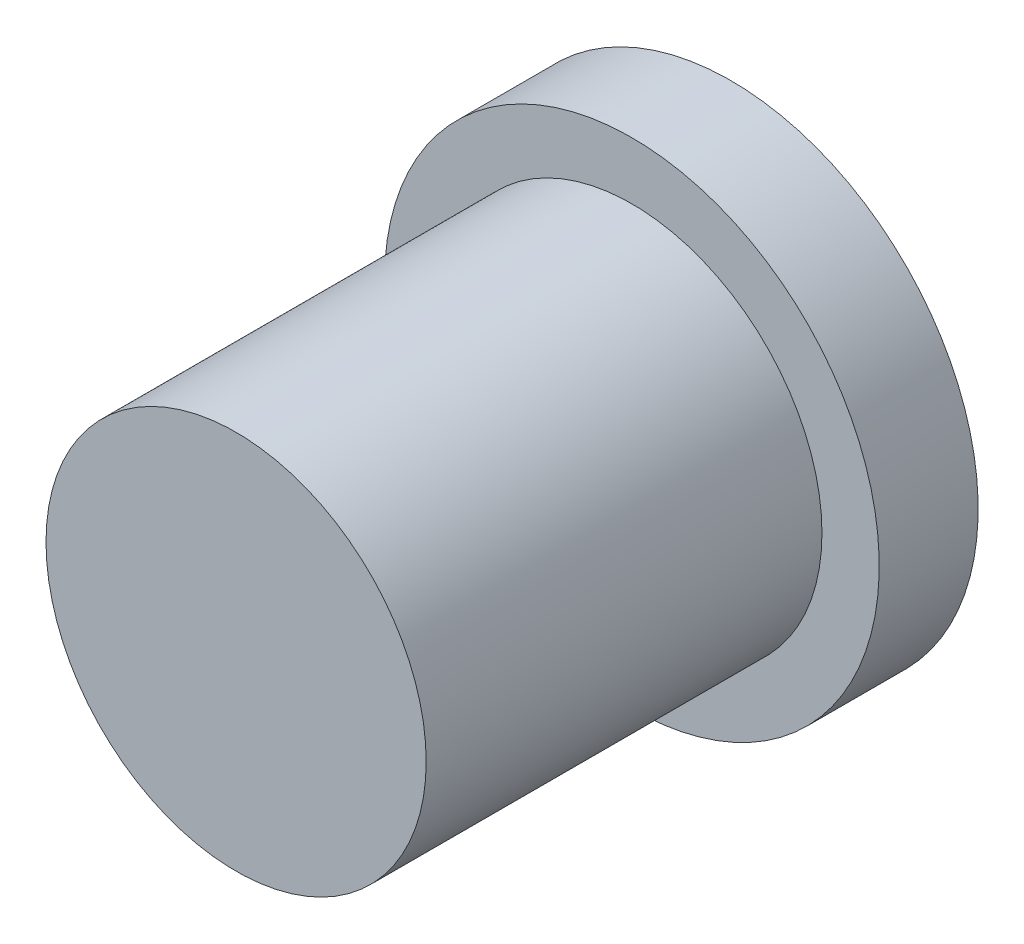
SolidWorks part; units mm, degrees
ref_plane "Front Plane" through (0, 0, 0) normal (0, 0, 1) x (1, 0, 0)
ref_plane "Top Plane" through (0, 0, 0) normal (0, 1, 0) x (1, 0, 0)
ref_plane "Right Plane" through (0, 0, 0) normal (1, 0, 0) x (0, 0, -1)
sketch "Sketch1" plane through (0, 0, 0) normal (0, 0, 1) x (1, 0, 0)
  circle A0 centre (0, 0) radius 6.35
  dimension "D1" = 12.7
extrude "Boss-Extrude1" add sketch "Sketch1" along normal blind 12.7 contours A0
sketch "Sketch2" plane through (0, 0, 0) normal (0, 0, -1) x (-1, 0, 0)
  circle A0 centre (0, 0) radius 7.9375
  dimension "D1" = 15.875
extrude "Boss-Extrude2" add sketch "Sketch2" along normal blind 3.175
other "Move Face1" face at (6.35, 0, 12.7) parameters "D1"=0.25
